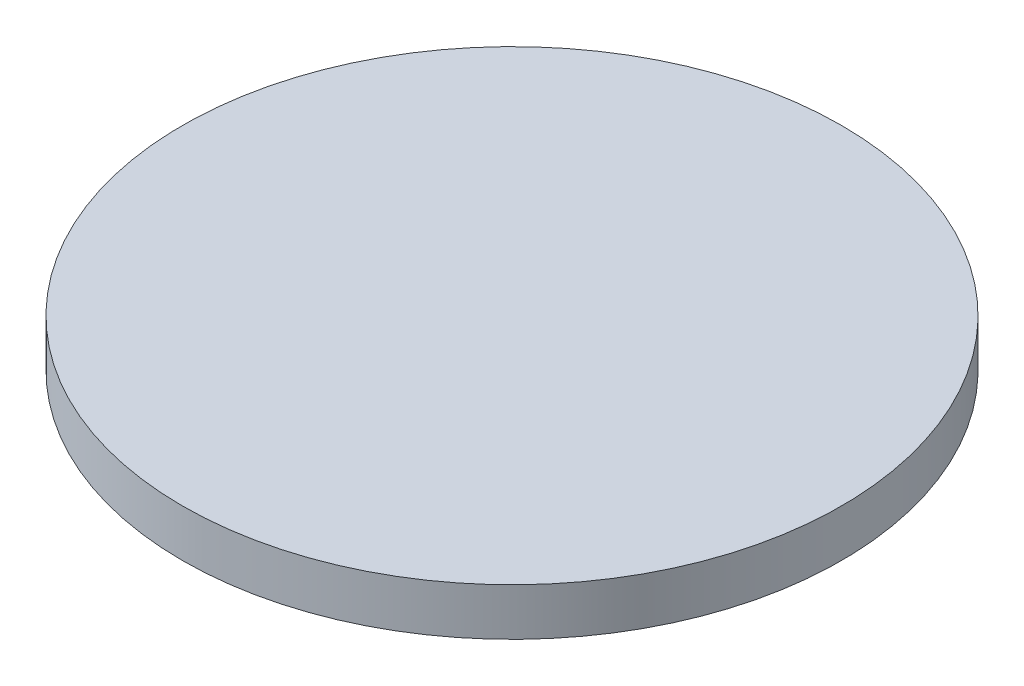
SolidWorks part; units mm, degrees
ref_plane "Front Plane" through (0, 0, 0) normal (0, 0, 1) x (1, 0, 0)
ref_plane "Top Plane" through (0, 0, 0) normal (0, 1, 0) x (1, 0, 0)
ref_plane "Right Plane" through (0, 0, 0) normal (1, 0, 0) x (0, 0, -1)
sketch "Sketch1" plane through (0, 0, 0) normal (0, 1, 0) x (1, 0, 0)
  circle A0 centre (0, 0) radius 10.45
  dimension "D1" = 20.9
extrude "Boss-Extrude1" add sketch "Sketch1" along normal blind 1.5
